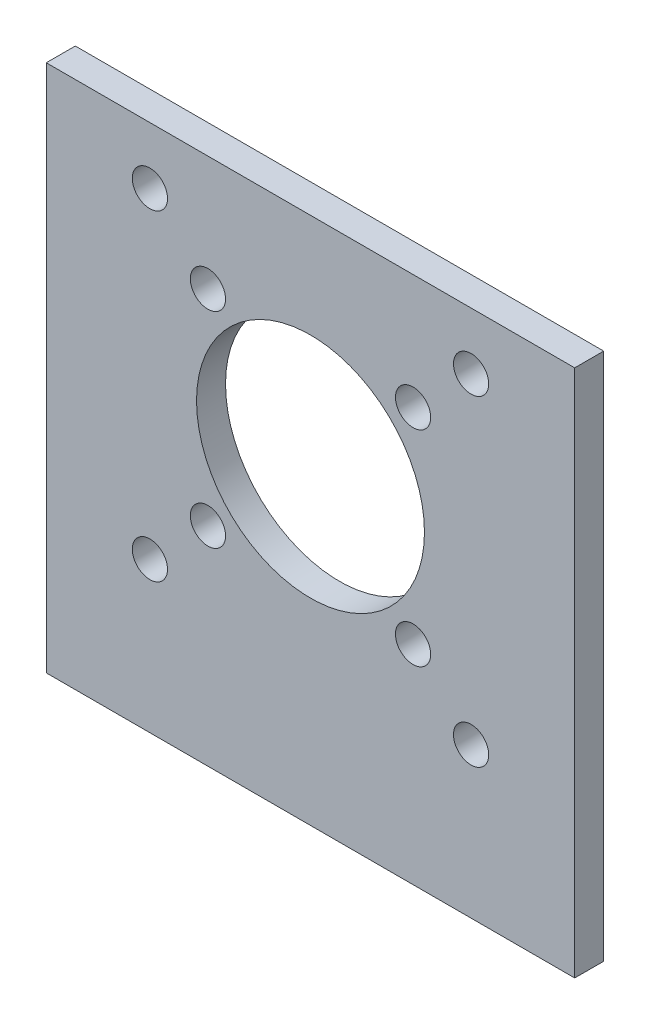
SolidWorks part; units mm, degrees
ref_plane "Front" through (0, 0, 0) normal (0, 0, 1) x (1, 0, 0)
ref_plane "Top" through (0, 0, 0) normal (0, 1, 0) x (1, 0, 0)
ref_plane "Right" through (0, 0, 0) normal (1, 0, 0) x (0, 0, -1)
sketch "Sketch1" plane through (0, 0, 0) normal (0, 0, 1) x (1, 0, 0)
  line L1 (-25.5, 25.5) -> (25.5, 25.5)
  line L2 (-25.5, 25.5) -> (-25.5, -25.5)
  line L3 (-25.5, -25.5) -> (25.5, -25.5)
  line L4 (25.5, 25.5) -> (25.5, -25.5)
  line L5 (-25.5, 25.5) -> (25.5, -25.5) construction
  line L6 (-25.5, -25.5) -> (25.5, 25.5) construction
  point P0 (0, 0)
  dimension "D1" = 51
  dimension "D2" = 51
extrude "Boss-Extrude1" add sketch "Sketch1" along normal blind 2.8
sketch "Sketch2" plane through (0, 0, 0) normal (0, 0, -1) x (-1, 0, 0)
  line L0 (-25.5, -25.5) -> (-25.5, 25.5) construction
  line L1 (-25.5, 25.5) -> (25.5, 25.5) construction
  line L2 (-15.5, -11) -> (15.5, 20) construction
  line L3 (-15.5, 20) -> (15.5, -11) construction
  circle A0 centre (0, 4.5) radius 11
  circle A1 centre (-15.5, 20) radius 1.7
  circle A2 centre (15.5, 20) radius 1.7
  circle A3 centre (15.5, -11) radius 1.7
  circle A4 centre (-15.5, -11) radius 1.7
  circle A5 centre (-9.8995, 14.3995) radius 1.7
  circle A6 centre (9.8995, 14.3995) radius 1.7
  circle A7 centre (9.8995, -5.3995) radius 1.7
  circle A8 centre (-9.8995, -5.3995) radius 1.7
  dimension "D1" = 22
  dimension "D6" = 3.4
  dimension "D7" = 10
  dimension "D2" = 25.5
  dimension "D3" = 21
  dimension "D4" = 31
  dimension "D5" = 31
  dimension "D8" = 5.5
  dimension "D9" = 14
extrude "Cut-Extrude1" cut sketch "Sketch2" against normal through all contours A0 | A1 | A4 | A3 | A2 | A6 | A5 | A7 | A8
